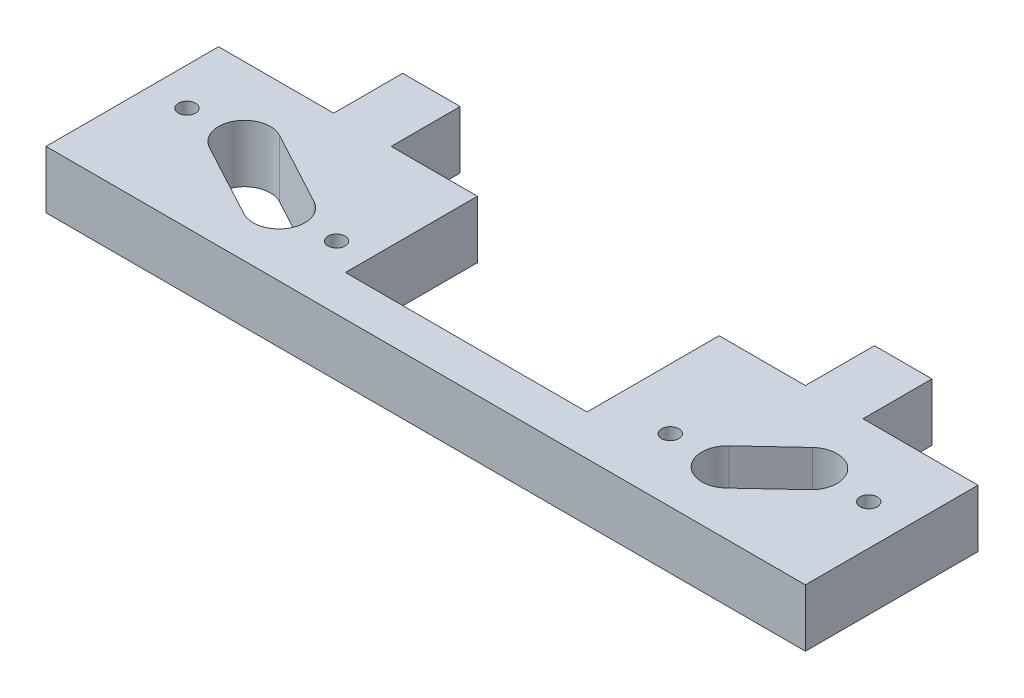
SolidWorks part; units mm, degrees
ref_plane "前视基准面" through (0, 0, 0) normal (0, 0, 1) x (1, 0, 0)
ref_plane "上视基准面" through (0, 0, 0) normal (0, 1, 0) x (1, 0, 0)
ref_plane "右视基准面" through (0, 0, 0) normal (1, 0, 0) x (0, 0, -1)
sketch "草图1" plane through (0, 0, 0) normal (0, 1, 0) x (1, 0, 0)
  line L16 (0, 0) -> (264, 0)
  line L17 (264, 0) -> (264, 60)
  line L18 (264, 60) -> (224, 60)
  line L19 (224, 60) -> (224, 84)
  line L20 (224, 84) -> (204, 84)
  line L21 (40, 84) -> (40, 60)
  line L22 (40, 60) -> (0, 60)
  line L23 (0, 60) -> (0, 0)
  line L24 (37.2669, 43.9242) -> (63.2669, 29.9242)
  line L25 (28.7331, 28.0758) -> (54.7331, 14.0758)
  line L26 (208.8591, 28.5795) -> (223.8591, 42.5795)
  line L27 (236.1409, 29.4205) -> (221.1409, 15.4205)
  line L28 (60, 84) -> (60, 60)
  line L29 (60, 60) -> (90, 60)
  line L30 (204, 60) -> (204, 84)
  line L31 (60, 84) -> (40, 84)
  line L32 (90, 60) -> (90, 14.0758)
  line L33 (90, 14.0758) -> (174, 14.0758)
  line L34 (174, 14.0758) -> (174, 60)
  line L35 (174, 60) -> (204, 60)
  arc A4 (37.2669, 43.9242) -> (28.7331, 28.0758) centre (33, 36) ccw
  arc A5 (54.7331, 14.0758) -> (63.2669, 29.9242) centre (59, 22) ccw
  arc A6 (208.8591, 28.5795) -> (221.1409, 15.4205) centre (215, 22) ccw
  arc A7 (236.1409, 29.4205) -> (223.8591, 42.5795) centre (230, 36) ccw
  circle A8 centre (33, 36) radius 20 construction
  circle A9 centre (59, 22) radius 20 construction
  circle A10 centre (215, 22) radius 20 construction
  circle A11 centre (230, 36) radius 20 construction
  circle A12 centre (13, 36) radius 3
  circle A13 centre (79, 22) radius 3
  circle A14 centre (195, 22) radius 3
  circle A15 centre (250, 36) radius 3
  dimension "D5" = 9
  dimension "D6" = 9
  dimension "D7" = 9
  dimension "D11" = 40
  dimension "D8" = 40
  dimension "D21" = 6
  dimension "D22" = 20
  dimension "D23" = 20
  dimension "D24" = 24
  dimension "D4" = 9
  dimension "D9" = 40
  dimension "D10" = 40
  dimension "D14" = 6
  dimension "D15" = 6
  dimension "D16" = 6
  dimension "D12" = 60
  dimension "D13" = 264
  dimension "D17" = 40
  dimension "D18" = 40
  dimension "D19" = 84
  dimension "D20" = 60
  dimension "D25" = 26
  dimension "D26" = 14
  dimension "D27" = 15
  dimension "D28" = 14
  dimension "D29" = 33
  dimension "D30" = 48
  dimension "D31" = 197
  dimension "D32" = 30
  dimension "D33" = 30
extrude "凸台-拉伸1" add sketch "草图1" along normal blind 20
